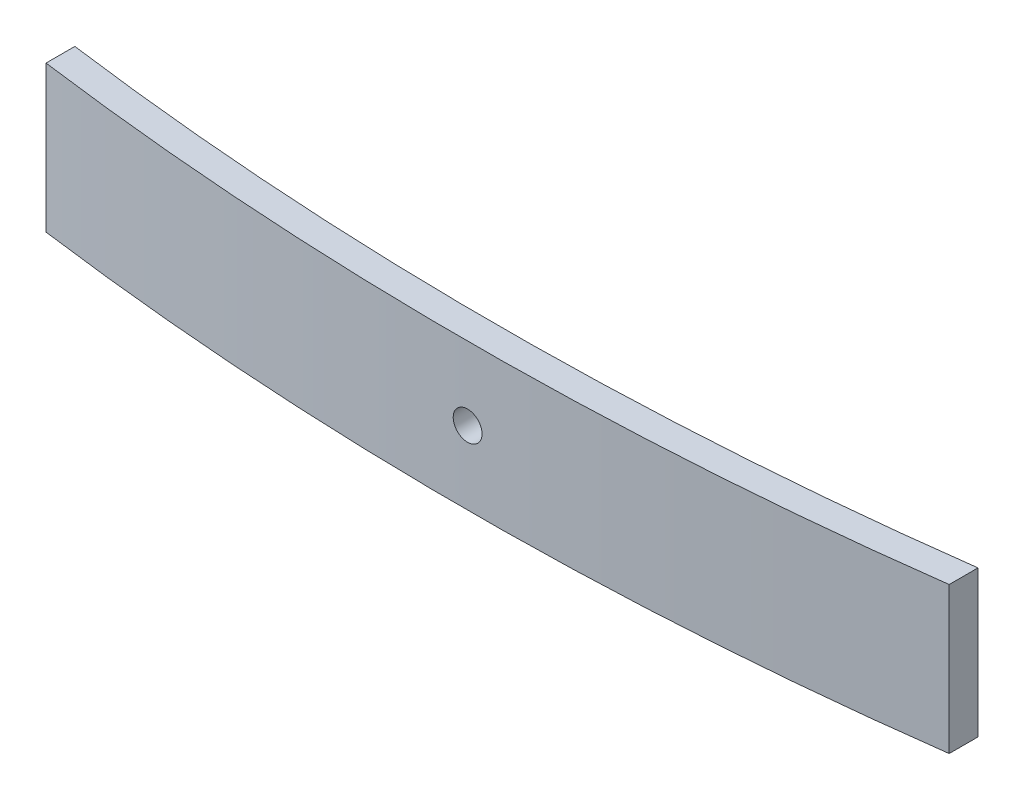
SolidWorks part; units mm, degrees
ref_plane "Front Plane" through (0, 0, 0) normal (0, 0, 1) x (1, 0, 0)
ref_plane "Top Plane" through (0, 0, 0) normal (0, 1, 0) x (1, 0, 0)
ref_plane "Right Plane" through (0, 0, 0) normal (1, 0, 0) x (0, 0, -1)
sketch "Sketch1" plane through (0, 0, 0) normal (0, 1, 0) x (1, 0, 0)
  line L0 (-630, 0) -> (630, 0) construction
  line L1 (-210.8013, -133) -> (245.5549, -133) construction
  line L2 (0, 0) -> (0, -133) construction
  line L3 (-602.5798, 17.4465) -> (-589.9243, 25.4988)
  line L4 (-616.835, -11.5296) -> (-605.5506, -21.4121)
  line L5 (616.835, -11.5296) -> (605.5506, -21.4121)
  line L6 (-630.0217, -47.5) -> (-630.0217, -62.5)
  line L7 (602.5798, 17.4465) -> (589.9243, 25.4988)
  line L8 (630.0217, -47.5) -> (630.0217, -62.5)
  line L9 (-545.0217, -92.3065) -> (-545.0217, -107.3065)
  line L10 (545.0217, -92.3065) -> (545.0217, -107.3065)
  line L11 (-485.0217, -125.4896) -> (-485.0217, -140.4896)
  line L12 (485.0217, -125.4896) -> (485.0217, -140.4896)
  line L13 (-425.0217, -156.3949) -> (-425.0217, -171.3949)
  line L14 (425.0217, -156.3949) -> (425.0217, -171.3949)
  line L15 (-315.0217, -194.8387) -> (-315.0217, -209.8387)
  line L16 (315.0217, -194.8387) -> (315.0217, -209.8387)
  line L17 (-275.0217, -216.5772) -> (-275.0217, -231.5772)
  line L18 (275.0217, -216.5772) -> (275.0217, -231.5772)
  line L19 (-235.0217, -237.3813) -> (-235.0217, -252.3813)
  line L20 (235.0217, -237.3813) -> (235.0217, -252.3813)
  arc A0 (-616.835, -11.5296) -> (-630, -17.5) centre (-630, 0) ccw
  arc A1 (630, -17.5) -> (616.835, -11.5296) centre (630, 0) ccw
  arc A2 (-630, -17.5) -> (630, -17.5) centre (0, 1642.9318) ccw
  arc A3 (-630.0011, -32.5) -> (630.0011, -32.5) centre (0, 1627.9379) ccw
  arc A4 (-605.5506, -21.4121) -> (-630.0011, -32.5) centre (-630, 0) ccw
  arc A5 (630.0011, -32.5) -> (605.5506, -21.4121) centre (630, 0) ccw
  arc A6 (-630.0217, -47.5) -> (630.0217, -47.5) centre (0, 1613.05) ccw
  arc A7 (630.0217, -47.5) -> (589.9243, 25.4988) centre (630, 0) ccw
  arc A8 (-589.9243, 25.4988) -> (-630.0217, -47.5) centre (-630, 0) ccw
  arc A9 (-630.0217, -62.5) -> (630.0217, -62.5) centre (0, 1598.05) ccw
  arc A10 (545.0217, -107.3065) -> (-545.0217, -107.3065) centre (0, 1583.05) cw
  arc A11 (485.0217, -140.4896) -> (-485.0217, -140.4896) centre (0, 1568.05) cw
  arc A12 (425.0217, -171.3949) -> (-425.0217, -171.3949) centre (0, 1553.05) cw
  arc A13 (315.0217, -209.8387) -> (-315.0217, -209.8387) centre (0, 1538.05) cw
  arc A14 (275.0217, -231.5772) -> (-275.0217, -231.5772) centre (0, 1523.05) cw
  arc A15 (235.0217, -252.3813) -> (-235.0217, -252.3813) centre (0, 1508.05) cw
  point P5 (-630.0217, -47.5)
  point P6 (0, -163)
  point P10 (0, -133)
  point P13 (-630.0011, -32.5)
  point P14 (0, -148)
  point P15 (630.0011, -32.5)
  point P20 (630.0217, -47.5)
  point P27 (0, -178)
  point P37 (0, -193)
  point P40 (630.0217, -55)
  point P44 (0, -208)
  point P50 (0, -223)
  point P56 (0, -238)
  point P62 (0, -253)
  point P68 (0, -268)
  dimension "D4" = 35
  dimension "D5" = 35
  dimension "D9" = 15
  dimension "D12" = 15
  dimension "D1" = 133
  dimension "D2" = 630
  dimension "D3" = 630
  dimension "D6" = 15
  dimension "D7" = 15
  dimension "D8" = 15
  dimension "D10" = 15
  dimension "D11" = 15
  dimension "D13" = 15
  dimension "D14" = 15
  dimension "D15" = 15
  dimension "D16" = 85
  dimension "D17" = 15
  dimension "D18" = 15
  dimension "D19" = 85
  dimension "D20" = 60
  dimension "D21" = 15
  dimension "D22" = 15
  dimension "D23" = 15
  dimension "D24" = 60
  dimension "D25" = 15
  dimension "D26" = 60
  dimension "D27" = 15
  dimension "D28" = 60
  dimension "D29" = 15
  dimension "D30" = 15
  dimension "D31" = 110
  dimension "D32" = 15
  dimension "D33" = 110
  dimension "D34" = 15
  dimension "D35" = 40
  dimension "D36" = 15
  dimension "D37" = 15
  dimension "D38" = 40
  dimension "D39" = 15
  dimension "D40" = 15
  dimension "D41" = 40
  dimension "D42" = 15
  dimension "D43" = 15
  dimension "D44" = 40
sketch "Sketch5" plane through (0, 0, 0) normal (0, 0, 1) x (1, 0, 0)
  circle A0 centre (0, 38.1) radius 7.5
  dimension "D2" = 15
  dimension "D1" = 38.1
sketch "Sketch6" plane through (0, 0, 0) normal (0, 0, 1) x (1, 0, 0)
  circle A0 centre (0, 38.1) radius 7.5
sketch "Sketch7" plane through (0, 0, 0) normal (0, 0, 1) x (1, 0, 0)
  circle A0 centre (0, 38.1) radius 7.5
sketch "Sketch8" plane through (0, 0, 0) normal (0, 0, 1) x (1, 0, 0)
  circle A0 centre (0, 38.1) radius 7.5
sketch "Sketch9" plane through (0, 0, 0) normal (0, 0, 1) x (1, 0, 0)
  circle A0 centre (0, 38.1) radius 7.5
sketch "Sketch10" plane through (0, 0, 0) normal (0, 0, 1) x (1, 0, 0)
  circle A0 centre (0, 38.1) radius 7.5
sketch "Sketch11" plane through (0, 0, 0) normal (0, 0, 1) x (1, 0, 0)
  circle A0 centre (0, 38.1) radius 7.5
sketch "Sketch12" plane through (0, 0, 0) normal (0, 0, 1) x (1, 0, 0)
  circle A0 centre (0, 38.1) radius 7.5
extrude "Boss-Extrude1" add sketch "Sketch1" along normal blind 76.2 contours A15 L20 A14 L19
sketch "Sketch13" plane through (0, 0, 0) normal (0, 0, 1) x (1, 0, 0)
  circle A0 centre (0, 38.1) radius 7.5
extrude "Cut-Extrude1" cut sketch "Sketch13" along normal through all
